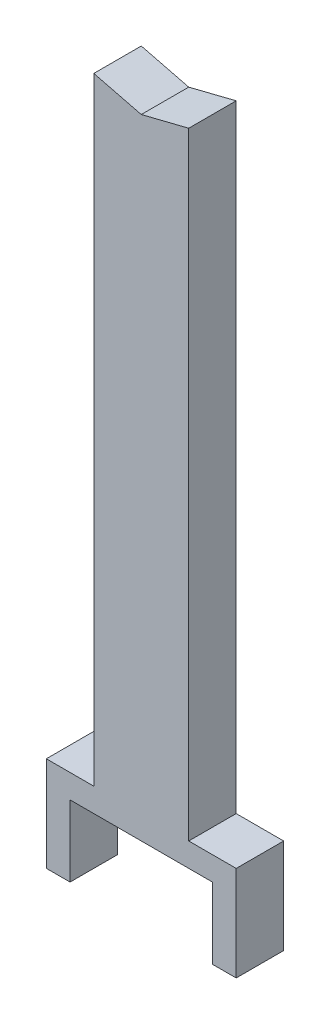
SolidWorks part; units mm, degrees
ref_plane "Front Plane" through (0, 0, 0) normal (0, 0, 1) x (1, 0, 0)
ref_plane "Top Plane" through (0, 0, 0) normal (0, 1, 0) x (1, 0, 0)
ref_plane "Right Plane" through (0, 0, 0) normal (1, 0, 0) x (0, 0, -1)
sketch "Sketch1" plane through (0, 0, 0) normal (0, 0, 1) x (1, 0, 0)
  line L0 (-50.8, 762.254) -> (0, 749.554)
  line L2 (-50.8, 101.6) -> (-50.8, 762.254)
  line L4 (50.8, 101.6) -> (50.8, 762.254)
  line L5 (0, 749.554) -> (50.8, 762.254)
  line L6 (0, 749.554) -> (0, 0) construction
  line L11 (-76.2, 0) -> (-76.2, 76.2)
  line L12 (-76.2, 76.2) -> (0, 76.2)
  line L13 (-76.2, 0) -> (-101.6, 0)
  line L14 (-101.6, 0) -> (-101.6, 101.6)
  line L15 (-101.6, 101.6) -> (-50.8, 101.6)
  line L17 (101.6, 101.6) -> (50.8, 101.6)
  line L18 (101.6, 0) -> (101.6, 101.6)
  line L19 (76.2, 0) -> (101.6, 0)
  line L20 (76.2, 0) -> (76.2, 76.2)
  line L21 (76.2, 76.2) -> (0, 76.2)
  point P0 (-76.2, 38.1)
  dimension "D1" = 203.2
  dimension "D2" = 101.6
  dimension "D3" = 12.7
  dimension "D4" = 101.6
  dimension "D5" = 25.4
  dimension "D6" = 25.4
  dimension "D7" = 762.254
extrude "Boss-Extrude1" add sketch "Sketch1" along normal mid plane 50.8
